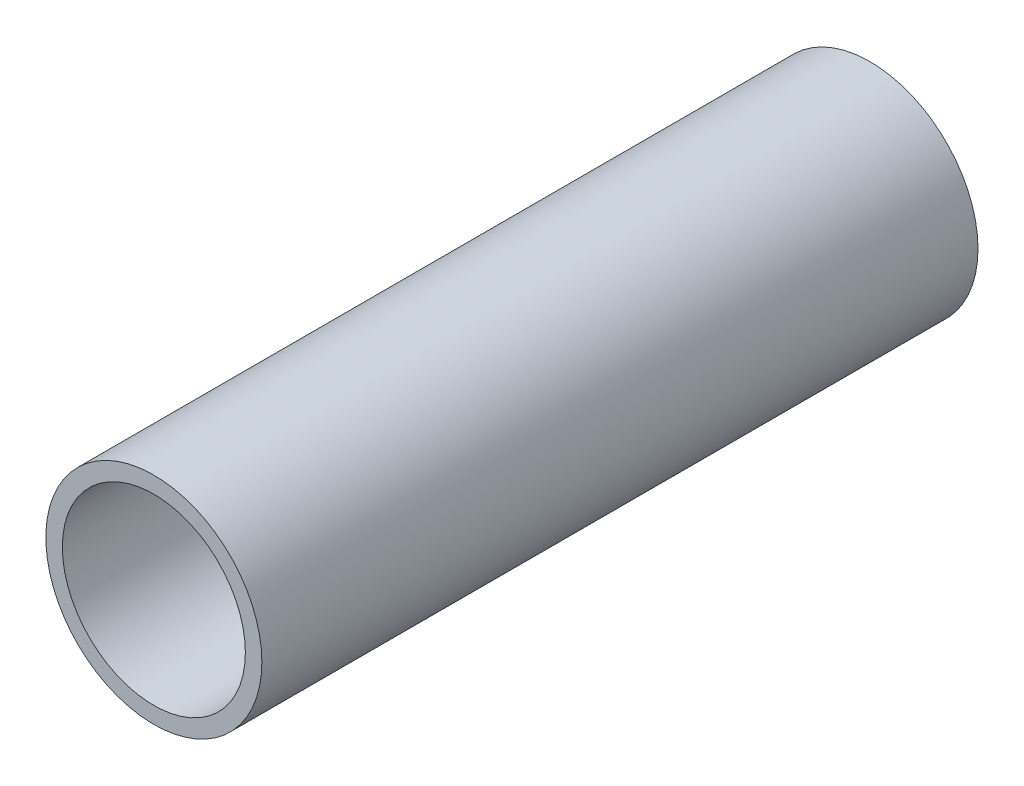
SolidWorks part; units mm, degrees
ref_plane "Front Plane" through (0, 0, 0) normal (0, 0, 1) x (1, 0, 0)
ref_plane "Top Plane" through (0, 0, 0) normal (0, 1, 0) x (1, 0, 0)
ref_plane "Right Plane" through (0, 0, 0) normal (1, 0, 0) x (0, 0, -1)
sketch "Sketch1" plane through (0, 0, 0) normal (0, 0, 1) x (1, 0, 0)
  circle A0 centre (0, 0) radius 24.13
  dimension "Pipe OD" = 48.26
extrude "Extrude-Thin1" add sketch "Sketch1" along normal mid plane 160 thin thin type one direction reverse wall 3.683
